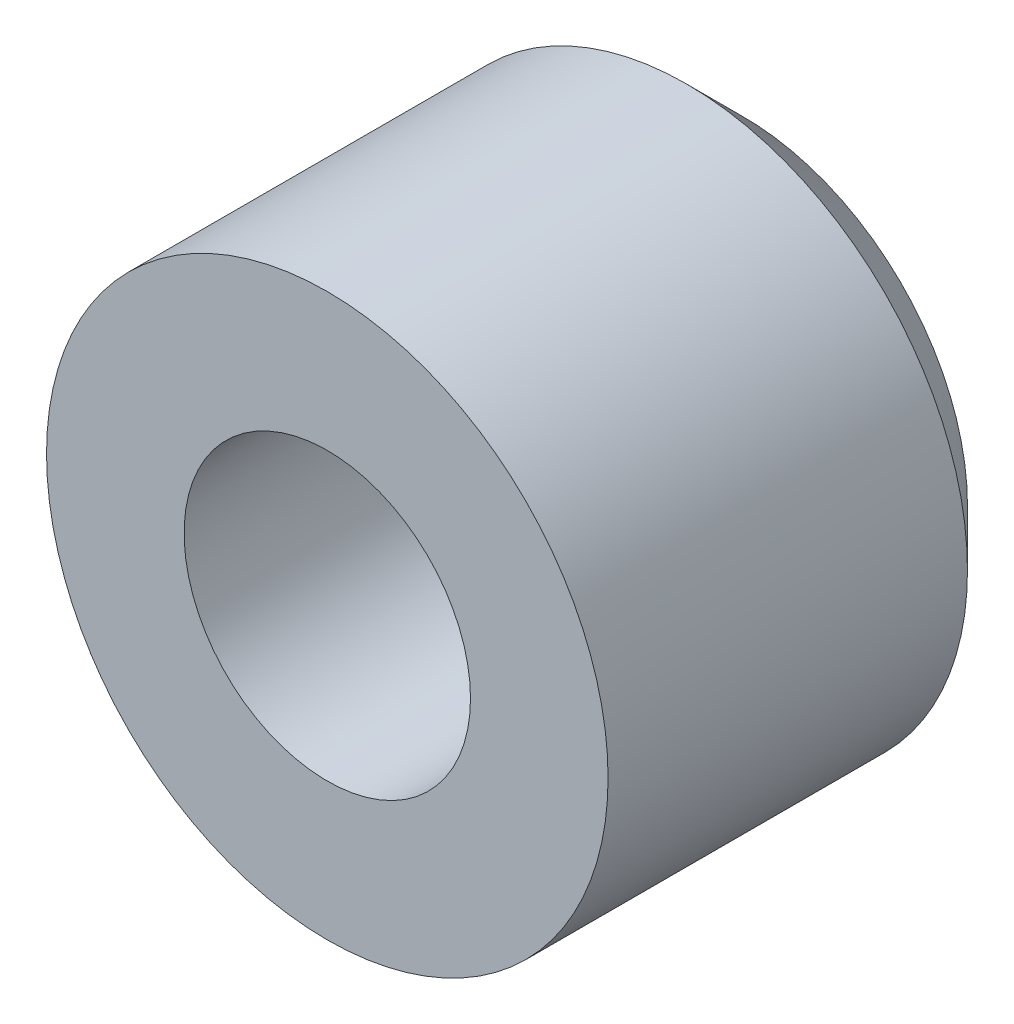
SolidWorks part; units mm, degrees
material "6061-T6 (SS)"
ref_plane "Спереди" through (0, 0, 0) normal (0, 0, 1) x (1, 0, 0)
ref_plane "Сверху" through (0, 0, 0) normal (0, 1, 0) x (1, 0, 0)
ref_plane "Справа" through (0, 0, 0) normal (1, 0, 0) x (0, 0, -1)
sketch "Эскиз1" plane through (0, 0, 0) normal (0, 0, 1) x (1, 0, 0)
  circle A0 centre (0, 0) radius 5
  circle A1 centre (0, 0) radius 2.55
  dimension "D1" = 10
  dimension "D2" = 5.1
extrude "Body" add sketch "Эскиз1" along normal blind 7.4
chamfer "Chamfer1" distance 1 angle 45 1 edges at (5, 0, 0)
